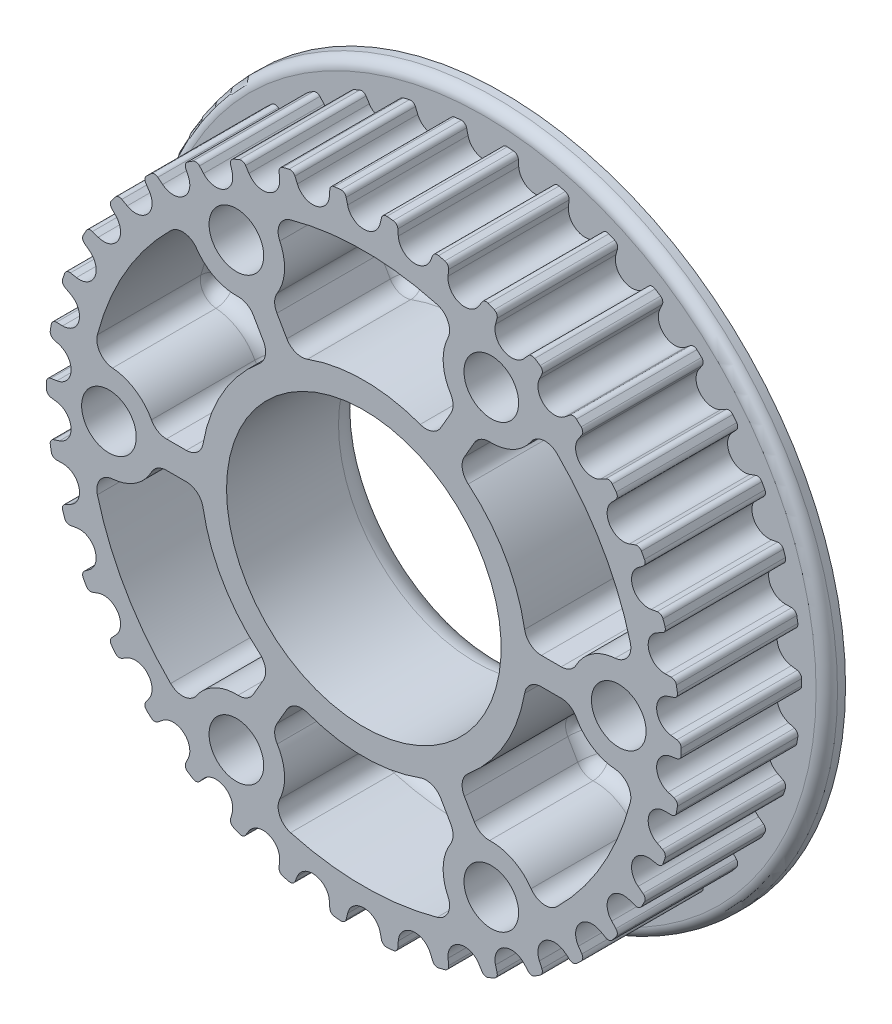
SolidWorks part; units mm, degrees
ref_plane "Front" through (0, 0, 0) normal (0, 0, 1) x (1, 0, 0)
ref_plane "Top" through (0, 0, 0) normal (0, 1, 0) x (1, 0, 0)
ref_plane "Right" through (0, 0, 0) normal (1, 0, 0) x (0, 0, -1)
sketch "Sketch1" plane through (0, 0, 0) normal (0, 1, 0) x (1, 0, 0)
  line L0 (32, 1.75) -> (0, 1.75)
  line L1 (0, 1.75) -> (0, 0)
  line L2 (0, 0) -> (32, 0)
  line L3 (32, 0) -> (32, 1.75)
  line L4 (0, 1.75) -> (0, 0) construction
revolve "Revolve1" add sketch "Sketch1" angle 360 about L4
sketch "Sketch2" plane through (0, 0, 0) normal (0, 0, 1) x (1, 0, 0)
  line L0 (7.9612, 28.5612) -> (7.8668, 27.5889)
  line L1 (10.7374, 26.6034) -> (11.2601, 27.4287)
  line L2 (12.5536, 26.8613) -> (12.3005, 25.9177)
  line L3 (14.9697, 24.4732) -> (15.6212, 25.2012)
  line L4 (16.8036, 24.4287) -> (16.3987, 23.5397)
  line L5 (18.7937, 21.6755) -> (19.5561, 22.2863)
  line L6 (20.5953, 21.3297) -> (20.0495, 20.5195)
  line L7 (22.1051, 18.2865) -> (22.9576, 18.7636)
  line L8 (23.8252, 17.6489) -> (23.1535, 16.9396)
  line L9 (24.8135, 14.3988) -> (25.7329, 14.7289)
  line L10 (26.4051, 13.4867) -> (25.6258, 12.8976)
  line L11 (26.845, 10.1182) -> (27.8062, 10.2926)
  line L12 (28.2648, 8.9566) -> (27.3992, 8.5038)
  line L13 (28.1443, 5.5617) -> (29.1211, 5.5754)
  line L14 (29.3536, 4.1822) -> (28.4252, 3.8781)
  line L15 (28.6758, 0.8534) -> (29.6416, 0.7062)
  line L16 (29.6416, -0.7062) -> (28.6758, -0.8534)
  line L17 (28.4252, -3.8781) -> (29.3536, -4.1823)
  line L18 (29.1211, -5.5754) -> (28.1443, -5.5617)
  line L19 (27.3992, -8.5038) -> (28.2648, -8.9566)
  line L20 (27.8062, -10.2926) -> (26.845, -10.1182)
  line L21 (25.6258, -12.8976) -> (26.4051, -13.4867)
  line L22 (25.7329, -14.7289) -> (24.8135, -14.3988)
  line L23 (23.1535, -16.9396) -> (23.8252, -17.6489)
  line L24 (22.9576, -18.7636) -> (22.1051, -18.2865)
  line L25 (20.0495, -20.5195) -> (20.5953, -21.3297)
  line L26 (19.5561, -22.2863) -> (18.7937, -21.6755)
  line L27 (16.3987, -23.5397) -> (16.8036, -24.4287)
  line L28 (15.6212, -25.2012) -> (14.9697, -24.4732)
  line L29 (12.3005, -25.9177) -> (12.5536, -26.8613)
  line L30 (11.2601, -27.4287) -> (10.7374, -26.6034)
  line L31 (7.8668, -27.5889) -> (7.9612, -28.5612)
  line L32 (6.592, -28.9079) -> (6.2122, -28.0079)
  line L33 (3.2186, -28.5074) -> (3.1516, -29.482)
  line L34 (1.744, -29.5987) -> (1.5175, -28.6484)
  line L35 (-1.5175, -28.6484) -> (-1.744, -29.5987)
  line L36 (-3.1516, -29.482) -> (-3.2186, -28.5074)
  line L37 (-6.2122, -28.0079) -> (-6.592, -28.9079)
  line L38 (-7.9612, -28.5612) -> (-7.8668, -27.5889)
  line L39 (-10.7374, -26.6034) -> (-11.2601, -27.4287)
  line L40 (-12.5536, -26.8613) -> (-12.3005, -25.9177)
  line L41 (-14.9697, -24.4732) -> (-15.6212, -25.2012)
  line L42 (-16.8036, -24.4287) -> (-16.3987, -23.5397)
  line L43 (-18.7937, -21.6755) -> (-19.5561, -22.2863)
  line L44 (-20.5953, -21.3297) -> (-20.0495, -20.5195)
  line L45 (-22.1051, -18.2865) -> (-22.9576, -18.7636)
  line L46 (-23.8252, -17.6489) -> (-23.1535, -16.9396)
  line L47 (-24.8135, -14.3988) -> (-25.7329, -14.7289)
  line L48 (-26.4051, -13.4867) -> (-25.6258, -12.8976)
  line L49 (-26.845, -10.1182) -> (-27.8062, -10.2926)
  line L50 (-28.2648, -8.9566) -> (-27.3992, -8.5038)
  line L51 (-28.1443, -5.5617) -> (-29.1211, -5.5754)
  line L52 (-29.3536, -4.1822) -> (-28.4252, -3.8781)
  line L53 (-28.6758, -0.8534) -> (-29.6416, -0.7062)
  line L54 (-29.6416, 0.7062) -> (-28.6758, 0.8534)
  line L55 (-28.4252, 3.8781) -> (-29.3536, 4.1822)
  line L56 (-29.1211, 5.5754) -> (-28.1443, 5.5617)
  line L57 (-27.3992, 8.5038) -> (-28.2648, 8.9566)
  line L58 (-27.8062, 10.2926) -> (-26.845, 10.1182)
  line L59 (-25.6258, 12.8976) -> (-26.4051, 13.4867)
  line L60 (-25.7329, 14.7289) -> (-24.8135, 14.3988)
  line L61 (-23.1535, 16.9396) -> (-23.8252, 17.6489)
  line L62 (-22.9576, 18.7636) -> (-22.1051, 18.2865)
  line L63 (-20.0495, 20.5195) -> (-20.5953, 21.3297)
  line L64 (-19.5561, 22.2863) -> (-18.7937, 21.6755)
  line L65 (-16.3987, 23.5397) -> (-16.8036, 24.4287)
  line L66 (-15.6212, 25.2012) -> (-14.9697, 24.4732)
  line L67 (-12.3005, 25.9177) -> (-12.5536, 26.8613)
  line L68 (-11.2601, 27.4287) -> (-10.7374, 26.6034)
  line L69 (-7.8668, 27.5889) -> (-7.9612, 28.5612)
  line L70 (-6.592, 28.9079) -> (-6.2122, 28.0079)
  line L71 (-3.2186, 28.5074) -> (-3.1516, 29.482)
  line L72 (-1.744, 29.5987) -> (-1.5175, 28.6484)
  line L73 (1.5175, 28.6484) -> (1.744, 29.5987)
  line L74 (3.1516, 29.482) -> (3.2186, 28.5074)
  line L75 (6.2122, 28.0079) -> (6.592, 28.9079)
  arc A0 (6.592, 28.9079) -> (7.9612, 28.5612) centre (0, 0) cw
  arc A1 (7.8668, 27.5889) -> (10.7374, 26.6034) centre (9.4195, 27.4382) ccw
  arc A2 (11.2601, 27.4287) -> (12.5536, 26.8613) centre (0, 0) cw
  arc A3 (12.3005, 25.9177) -> (14.9697, 24.4732) centre (13.8072, 25.5135) ccw
  arc A4 (15.6212, 25.2012) -> (16.8036, 24.4287) centre (0, 0) cw
  arc A5 (16.3987, 23.5397) -> (18.7937, 21.6755) centre (17.8183, 22.893) ccw
  arc A6 (19.5561, 22.2863) -> (20.5953, 21.3297) centre (0, 0) cw
  arc A7 (20.0495, 20.5195) -> (22.1051, 18.2865) centre (21.3434, 19.6479) ccw
  arc A8 (22.9576, 18.7636) -> (23.8252, 17.6489) centre (0, 0) cw
  arc A9 (23.1535, 16.9396) -> (24.8135, 14.3988) centre (24.2862, 15.867) ccw
  arc A10 (25.7329, 14.7289) -> (26.4051, 13.4867) centre (0, 0) cw
  arc A11 (25.6258, 12.8976) -> (26.845, 10.1182) centre (26.5666, 11.6532) ccw
  arc A12 (27.8062, 10.2926) -> (28.2648, 8.9566) centre (0, 0) cw
  arc A13 (27.3992, 8.5038) -> (28.1443, 5.5617) centre (28.1223, 7.1215) ccw
  arc A14 (29.1211, 5.5754) -> (29.3536, 4.1822) centre (0, 0) cw
  arc A15 (28.4252, 3.8781) -> (28.6758, 0.8534) centre (28.9109, 2.3956) ccw
  arc A16 (29.6416, 0.7062) -> (29.6416, -0.7062) centre (0, 0) cw
  arc A17 (28.6758, -0.8534) -> (28.4252, -3.8781) centre (28.9109, -2.3956) ccw
  arc A18 (29.3536, -4.1823) -> (29.1211, -5.5754) centre (0, 0) cw
  arc A19 (28.1443, -5.5617) -> (27.3992, -8.5038) centre (28.1223, -7.1215) ccw
  arc A20 (28.2648, -8.9566) -> (27.8062, -10.2926) centre (0, 0) cw
  arc A21 (26.845, -10.1182) -> (25.6258, -12.8976) centre (26.5666, -11.6532) ccw
  arc A22 (26.4051, -13.4867) -> (25.7329, -14.7289) centre (0, 0) cw
  arc A23 (24.8135, -14.3988) -> (23.1535, -16.9396) centre (24.2862, -15.867) ccw
  arc A24 (23.8252, -17.6489) -> (22.9576, -18.7636) centre (0, 0) cw
  arc A25 (22.1051, -18.2865) -> (20.0495, -20.5195) centre (21.3433, -19.6479) ccw
  arc A26 (20.5953, -21.3297) -> (19.5561, -22.2863) centre (0, 0) cw
  arc A27 (18.7937, -21.6755) -> (16.3987, -23.5397) centre (17.8183, -22.893) ccw
  arc A28 (16.8036, -24.4287) -> (15.6212, -25.2012) centre (0, 0) cw
  arc A29 (14.9697, -24.4732) -> (12.3005, -25.9177) centre (13.8072, -25.5135) ccw
  arc A30 (12.5536, -26.8613) -> (11.2601, -27.4287) centre (0, 0) cw
  arc A31 (10.7374, -26.6034) -> (7.8668, -27.5889) centre (9.4195, -27.4382) ccw
  arc A32 (7.9612, -28.5612) -> (6.592, -28.9079) centre (0, 0) cw
  arc A33 (6.2122, -28.0079) -> (3.2186, -28.5074) centre (4.7749, -28.6143) ccw
  arc A34 (3.1516, -29.482) -> (1.744, -29.5987) centre (0, 0) cw
  arc A35 (1.5175, -28.6484) -> (-1.5175, -28.6484) centre (0, -29.01) ccw
  arc A36 (-1.744, -29.5987) -> (-3.1516, -29.482) centre (0, 0) cw
  arc A37 (-3.2186, -28.5074) -> (-6.2122, -28.0079) centre (-4.7749, -28.6143) ccw
  arc A38 (-6.592, -28.9079) -> (-7.9612, -28.5612) centre (0, 0) cw
  arc A39 (-7.8668, -27.5889) -> (-10.7374, -26.6034) centre (-9.4195, -27.4382) ccw
  arc A40 (-11.2601, -27.4287) -> (-12.5536, -26.8613) centre (0, 0) cw
  arc A41 (-12.3005, -25.9177) -> (-14.9697, -24.4732) centre (-13.8072, -25.5135) ccw
  arc A42 (-15.6212, -25.2012) -> (-16.8036, -24.4287) centre (0, 0) cw
  arc A43 (-16.3987, -23.5397) -> (-18.7937, -21.6755) centre (-17.8183, -22.893) ccw
  arc A44 (-19.5561, -22.2863) -> (-20.5953, -21.3297) centre (0, 0) cw
  arc A45 (-20.0495, -20.5195) -> (-22.1051, -18.2865) centre (-21.3434, -19.6479) ccw
  arc A46 (-22.9576, -18.7636) -> (-23.8252, -17.6489) centre (0, 0) cw
  arc A47 (-23.1535, -16.9396) -> (-24.8135, -14.3988) centre (-24.2862, -15.867) ccw
  arc A48 (-25.7329, -14.7289) -> (-26.4051, -13.4867) centre (0, 0) cw
  arc A49 (-25.6258, -12.8976) -> (-26.845, -10.1182) centre (-26.5666, -11.6532) ccw
  arc A50 (-27.8062, -10.2926) -> (-28.2648, -8.9566) centre (0, 0) cw
  arc A51 (-27.3992, -8.5038) -> (-28.1443, -5.5617) centre (-28.1223, -7.1215) ccw
  arc A52 (-29.1211, -5.5754) -> (-29.3536, -4.1822) centre (0, 0) cw
  arc A53 (-28.4252, -3.8781) -> (-28.6758, -0.8534) centre (-28.9109, -2.3956) ccw
  arc A54 (-29.6416, -0.7062) -> (-29.6416, 0.7062) centre (0, 0) cw
  arc A55 (-28.6758, 0.8534) -> (-28.4252, 3.8781) centre (-28.9109, 2.3956) ccw
  arc A56 (-29.3536, 4.1822) -> (-29.1211, 5.5754) centre (0, 0) cw
  arc A57 (-28.1443, 5.5617) -> (-27.3992, 8.5038) centre (-28.1223, 7.1215) ccw
  arc A58 (-28.2648, 8.9566) -> (-27.8062, 10.2926) centre (0, 0) cw
  arc A59 (-26.845, 10.1182) -> (-25.6258, 12.8976) centre (-26.5666, 11.6532) ccw
  arc A60 (-26.4051, 13.4867) -> (-25.7329, 14.7289) centre (0, 0) cw
  arc A61 (-24.8135, 14.3988) -> (-23.1535, 16.9396) centre (-24.2862, 15.867) ccw
  arc A62 (-23.8252, 17.6489) -> (-22.9576, 18.7636) centre (0, 0) cw
  arc A63 (-22.1051, 18.2865) -> (-20.0495, 20.5195) centre (-21.3434, 19.6479) ccw
  arc A64 (-20.5953, 21.3297) -> (-19.5561, 22.2863) centre (0, 0) cw
  arc A65 (-18.7937, 21.6755) -> (-16.3987, 23.5397) centre (-17.8183, 22.893) ccw
  arc A66 (-16.8036, 24.4287) -> (-15.6212, 25.2012) centre (0, 0) cw
  arc A67 (-14.9697, 24.4732) -> (-12.3005, 25.9177) centre (-13.8072, 25.5135) ccw
  arc A68 (-12.5536, 26.8613) -> (-11.2601, 27.4287) centre (0, 0) cw
  arc A69 (-10.7374, 26.6034) -> (-7.8668, 27.5889) centre (-9.4195, 27.4382) ccw
  arc A70 (-7.9612, 28.5612) -> (-6.592, 28.9079) centre (0, 0) cw
  arc A71 (-6.2122, 28.0079) -> (-3.2186, 28.5074) centre (-4.7749, 28.6143) ccw
  arc A72 (-3.1516, 29.482) -> (-1.744, 29.5987) centre (0, 0) cw
  arc A73 (-1.5175, 28.6484) -> (1.5175, 28.6484) centre (0, 29.01) ccw
  arc A74 (1.744, 29.5987) -> (3.1516, 29.482) centre (0, 0) cw
  arc A75 (3.2186, 28.5074) -> (6.2122, 28.0079) centre (4.7749, 28.6143) ccw
extrude "Boss-Extrude1" add sketch "Sketch2" along normal blind 11.25
sketch "Sketch3" plane through (0, 0, 11.25) normal (0, 0, 1) x (1, 0, 0)
  line L0 (-10.8476, -16.2485) -> (-8.6933, -12.5173)
  line L1 (-15.187, -1.27) -> (-19.4954, -1.27)
  arc A0 (-8.6933, -12.5173) -> (-15.187, -1.27) centre (0, 0) cw
  arc A1 (-19.4954, -1.27) -> (-25.3685, -4.2224) centre (-23.8125, 0) cw
  arc A2 (-25.3685, -4.2224) -> (-16.341, -19.8586) centre (0, 0) ccw
  arc A3 (-16.341, -19.8586) -> (-10.8476, -16.2485) centre (-11.9063, -20.6222) cw
extrude "Cut-Extrude1" cut sketch "Sketch3" against normal blind 11.25
sketch "Sketch4" plane through (0, 0, 11.25) normal (0, 0, 1) x (1, 0, 0)
  line L0 (8.6479, -17.5185) -> (6.4936, -13.7873)
  line L1 (-6.4936, -13.7873) -> (-8.6479, -17.5185)
  arc A0 (6.4936, -13.7873) -> (-6.4936, -13.7873) centre (0, 0) cw
  arc A1 (-8.6479, -17.5185) -> (-9.0275, -24.081) centre (-11.9063, -20.6222) cw
  arc A2 (-9.0275, -24.081) -> (9.0275, -24.081) centre (0, 0) ccw
  arc A3 (9.0275, -24.081) -> (8.6479, -17.5185) centre (11.9062, -20.6222) cw
extrude "Cut-Extrude2" cut sketch "Sketch4" against normal blind 11.25
sketch "Sketch5" plane through (0, 0, 11.25) normal (0, 0, 1) x (1, 0, 0)
  line L0 (8.6933, -12.5173) -> (10.8476, -16.2485)
  line L1 (19.4954, -1.27) -> (15.187, -1.27)
  arc A0 (15.187, -1.27) -> (8.6933, -12.5173) centre (0, 0) cw
  arc A1 (10.8476, -16.2485) -> (16.341, -19.8586) centre (11.9062, -20.6222) cw
  arc A2 (16.341, -19.8586) -> (25.3685, -4.2224) centre (0, 0) ccw
  arc A3 (25.3685, -4.2224) -> (19.4954, -1.27) centre (23.8125, 0) cw
extrude "Cut-Extrude3" cut sketch "Sketch5" against normal blind 11.25
sketch "Sketch6" plane through (0, 0, 11.25) normal (0, 0, 1) x (1, 0, 0)
  line L0 (15.187, 1.27) -> (19.4954, 1.27)
  line L1 (10.8476, 16.2485) -> (8.6933, 12.5173)
  arc A0 (8.6933, 12.5173) -> (15.187, 1.27) centre (0, 0) cw
  arc A1 (19.4954, 1.27) -> (25.3685, 4.2224) centre (23.8125, 0) cw
  arc A2 (25.3685, 4.2224) -> (16.341, 19.8586) centre (0, 0) ccw
  arc A3 (16.341, 19.8586) -> (10.8476, 16.2485) centre (11.9063, 20.6222) cw
extrude "Cut-Extrude4" cut sketch "Sketch6" against normal blind 11.25
sketch "Sketch7" plane through (0, 0, 11.25) normal (0, 0, 1) x (1, 0, 0)
  line L0 (6.4936, 13.7873) -> (8.6479, 17.5185)
  line L1 (-8.6479, 17.5185) -> (-6.4936, 13.7873)
  arc A0 (-6.4936, 13.7873) -> (6.4936, 13.7873) centre (0, 0) cw
  arc A1 (8.6479, 17.5185) -> (9.0275, 24.081) centre (11.9063, 20.6222) cw
  arc A2 (9.0275, 24.081) -> (-9.0275, 24.081) centre (0, 0) ccw
  arc A3 (-9.0275, 24.081) -> (-8.6479, 17.5185) centre (-11.9062, 20.6222) cw
extrude "Cut-Extrude5" cut sketch "Sketch7" against normal blind 11.25
sketch "Sketch8" plane through (0, 0, 11.25) normal (0, 0, 1) x (1, 0, 0)
  line L0 (-19.4954, 1.27) -> (-15.187, 1.27)
  line L1 (-8.6933, 12.5173) -> (-10.8476, 16.2485)
  arc A0 (-15.187, 1.27) -> (-8.6933, 12.5173) centre (0, 0) cw
  arc A1 (-10.8476, 16.2485) -> (-16.341, 19.8586) centre (-11.9062, 20.6222) cw
  arc A2 (-16.341, 19.8586) -> (-25.3685, 4.2224) centre (0, 0) ccw
  arc A3 (-25.3685, 4.2224) -> (-19.4954, 1.27) centre (-23.8125, 0) cw
extrude "Cut-Extrude6" cut sketch "Sketch8" against normal blind 11.25
hole_wizard "#7 (0.201) Diameter Hole1" positions "Sketch10" profile "Sketch9" hole size "#7" standard "ANSI Inch"
sketch "Sketch10" plane through (0, 0, 11.25) normal (0, 0, 1) x (1, 0, 0)
  point P0 (23.8125, 0)
  point P1 (11.9062, 20.6222)
  point P2 (-11.9062, 20.6222)
  point P3 (-23.8125, 0)
  point P4 (-11.9062, -20.6222)
  point P5 (11.9062, -20.6222)
sketch "Sketch9" plane through (23.8125, 0, 11.25) normal (1, 0, 0) x (0, -1, 0)
  line L0 (0, 0) -> (0, 13)
  line L1 (0, 13) -> (2.5527, 13)
  line L2 (2.5527, 13) -> (2.5527, 0)
  line L5 (2.5527, 0) -> (0, 0)
  line L11 (0, -6.35) -> (0, 107.95) construction
  dimension "Thru Hole Dia." = 5.1054
  dimension "Thru Hole Depth" = 13
hole_wizard "Hole1" positions "Sketch12" profile "Sketch11" legacy
sketch "Sketch12" plane through (0, 0, -1.75) normal (0, 0, -1) x (-1, 0, 0)
  point P0 (0, 0)
sketch "Sketch11" plane through (0, 0, -1.75) normal (1, 0, 0) x (0, 1, 0)
  line L0 (0, 0) -> (0, 13)
  line L1 (0, 13) -> (12.827, 13)
  line L2 (12.827, 13) -> (12.827, 0)
  line L3 (12.827, 0) -> (0, 0)
  line L4 (0, 110) -> (0, -10) construction
  dimension "Diameter" = 25.654
  dimension "Depth" = 13
fillet "Fillet1" radius 0.48 76 edges at (25.7329, 14.7289, 5.625) (20.5953, -21.3297, 5.625) (3.1516, -29.482, 5.625) (3.1516, 29.482, 5.625) (29.3536, -4.1823, 5.625) (-1.744, 29.5987, 5.625) (-6.592, -28.9079, 5.625) (-3.1516, 29.482, 5.625) (12.5536, -26.8613, 5.625) (-6.592, 28.9079, 5.625) (26.4051, -13.4867, 5.625) (-7.9612, 28.5612, 5.625) (29.1211, 5.5754, 5.625) (-11.2601, 27.4287, 5.625) (6.592, 28.9079, 5.625) (19.5561, 22.2863, 5.625) (-12.5536, 26.8613, 5.625) (-1.744, -29.5987, 5.625) (-15.6212, 25.2012, 5.625) (7.9612, -28.5612, 5.625) (-16.8036, 24.4287, 5.625) (16.8036, -24.4287, 5.625) (-19.5561, 22.2863, 5.625) (23.8252, -17.6489, 5.625) (-20.5953, 21.3297, 5.625) (28.2648, -8.9566, 5.625) (-22.9576, 18.7636, 5.625) (29.6416, 0.7062, 5.625) (-23.8252, 17.6489, 5.625) (27.8062, 10.2926, 5.625) (-25.7329, 14.7289, 5.625) (22.9576, 18.7636, 5.625) (-26.4051, 13.4867, 5.625) (15.6212, 25.2012, 5.625) (-27.8062, 10.2926, 5.625) (-7.9612, -28.5612, 5.625) (-28.2648, 8.9566, 5.625) (-3.1516, -29.482, 5.625) (1.744, 29.5987, 5.625) (1.744, -29.5987, 5.625) (-29.1211, 5.5754, 5.625) (6.592, -28.9079, 5.625) (-29.3536, 4.1822, 5.625) (11.2601, -27.4287, 5.625) (-29.6416, 0.7062, 5.625) (15.6212, -25.2012, 5.625) (-29.6416, -0.7062, 5.625) (19.5561, -22.2863, 5.625) (-29.3536, -4.1822, 5.625) (22.9576, -18.7636, 5.625) (-29.1211, -5.5754, 5.625) (25.7329, -14.7289, 5.625) (-28.2648, -8.9566, 5.625) (7.9612, 28.5612, 5.625) (-27.8062, -10.2926, 5.625) (29.1211, -5.5754, 5.625) (-26.4051, -13.4867, 5.625) (29.6416, -0.7062, 5.625) (-25.7329, -14.7289, 5.625) (29.3536, 4.1822, 5.625) (-23.8252, -17.6489, 5.625) (28.2648, 8.9566, 5.625) (-22.9576, -18.7636, 5.625) (26.4051, 13.4867, 5.625) (-20.5953, -21.3297, 5.625) (23.8252, 17.6489, 5.625) (-19.5561, -22.2863, 5.625) (20.5953, 21.3297, 5.625) (-16.8036, -24.4287, 5.625) (16.8036, 24.4287, 5.625) (-15.6212, -25.2012, 5.625) (12.5536, 26.8613, 5.625) (-12.5536, -26.8613, 5.625) (11.2601, 27.4287, 5.625) (-11.2601, -27.4287, 5.625) (27.8062, -10.2926, 5.625)
fillet "Fillet2" radius 1 1 edges at (32, 0, 0)
fillet "Fillet3" radius 1.5875 72 edges at (-6.4936, 13.7873, 5.625) (-7.5708, 15.6529, 0) (-8.6479, 17.5185, 5.625) (6.4936, 13.7873, 5.625) (0, 15.24, 0) (-7.4138, 20.8821, 0) (-9.0275, 24.081, 5.625) (7.5708, 15.6529, 0) (8.6479, 17.5185, 5.625) (0, 25.7175, 0) (7.4138, 20.8821, 0) (9.0275, 24.081, 5.625) (25.3685, -4.2224, 5.625) (19.4954, -1.27, 5.625) (21.7913, -4.0206, 0) (22.272, -12.8587, 0) (16.341, -19.8586, 5.625) (17.3412, -1.27, 0) (15.187, -1.27, 5.625) (10.8476, -16.2485, 5.625) (14.3776, -16.8616, 0) (13.1982, -7.62, 0) (9.7705, -14.3829, 0) (8.6933, -12.5173, 5.625) (-10.8476, -16.2485, 5.625) (-14.3776, -16.8616, 0) (-16.341, -19.8586, 5.625) (-8.6933, -12.5173, 5.625) (-9.7705, -14.3829, 0) (-22.272, -12.8587, 0) (-25.3685, -4.2224, 5.625) (-13.1982, -7.62, 0) (-15.187, -1.27, 5.625) (-21.7913, -4.0206, 0) (-17.3412, -1.27, 0) (-19.4954, -1.27, 5.625) (19.4954, 1.27, 5.625) (15.187, 1.27, 5.625) (17.3412, 1.27, 0) (25.3685, 4.2224, 5.625) (21.7913, 4.0206, 0) (13.1982, 7.62, 0) (8.6933, 12.5173, 5.625) (22.272, 12.8587, 0) (16.341, 19.8586, 5.625) (9.7705, 14.3829, 0) (14.3776, 16.8616, 0) (10.8476, 16.2485, 5.625) (-8.6479, -17.5185, 5.625) (-6.4936, -13.7873, 5.625) (-7.5708, -15.6529, 0) (-9.0275, -24.081, 5.625) (-7.4138, -20.8821, 0) (0, -15.24, 0) (6.4936, -13.7873, 5.625) (0, -25.7175, 0) (9.0275, -24.081, 5.625) (7.5708, -15.6529, 0) (7.4138, -20.8821, 0) (8.6479, -17.5185, 5.625) (-10.8476, 16.2485, 5.625) (-8.6933, 12.5173, 5.625) (-9.7705, 14.3829, 0) (-16.341, 19.8586, 5.625) (-14.3776, 16.8616, 0) (-13.1982, 7.62, 0) (-15.187, 1.27, 5.625) (-22.272, 12.8588, 0) (-25.3685, 4.2224, 5.625) (-17.3412, 1.27, 0) (-21.7913, 4.0206, 0) (-19.4954, 1.27, 5.625)
fillet "Fillet4" radius 2.54 1 edges at (-12.827, 0, -1.75)
